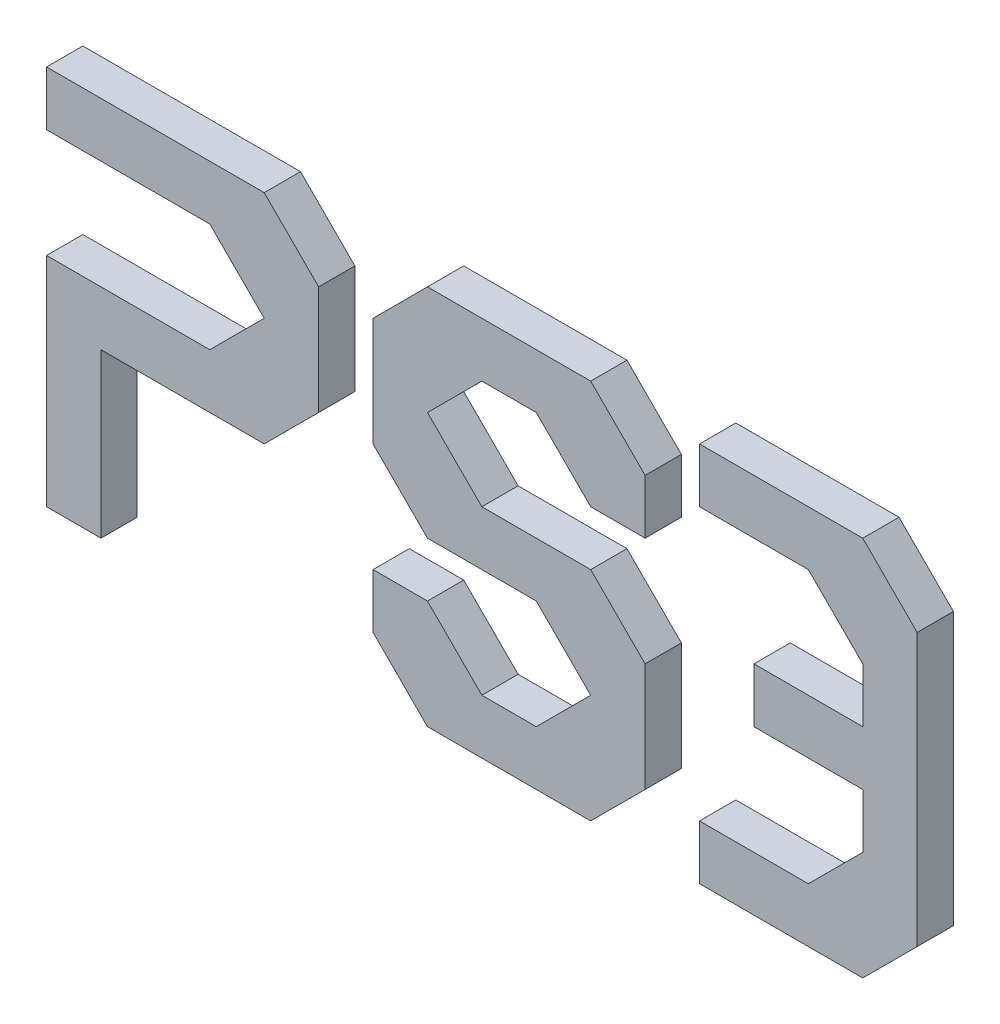
SolidWorks part; units mm, degrees
ref_plane "Front Plane" through (0, 0, 0) normal (0, 0, 1) x (1, 0, 0)
ref_plane "Top Plane" through (0, 0, 0) normal (0, 1, 0) x (1, 0, 0)
ref_plane "Right Plane" through (0, 0, 0) normal (1, 0, 0) x (0, 0, -1)
sketch "Sketch1" plane through (0, 0, 0) normal (0, 0, 1) x (1, 0, 0)
  line L0 (15, 15) -> (30, 15)
  line L1 (0, 0) -> (15, 0)
  line L2 (0, 0) -> (0, 15)
  line L3 (0, 15) -> (15, 15)
  line L4 (15, 0) -> (15, 15)
  line L5 (30, 0) -> (30, 15)
  line L6 (15, 0) -> (30, 0)
  line L7 (15, 0) -> (15, 15)
  line L8 (30, 15) -> (45, 15)
  line L9 (45, 0) -> (45, 15)
  line L10 (30, 0) -> (45, 0)
  line L11 (30, 0) -> (30, 15)
  line L12 (45, 15) -> (60, 15)
  line L13 (60, 0) -> (60, 15)
  line L14 (45, 0) -> (60, 0)
  line L15 (45, 0) -> (45, 15)
  line L16 (60, 15) -> (75, 15)
  line L17 (75, 0) -> (75, 15)
  line L18 (60, 0) -> (75, 0)
  line L19 (60, 0) -> (60, 15)
  line L20 (75, 15) -> (90, 15)
  line L21 (90, 0) -> (90, 15)
  line L22 (75, 0) -> (90, 0)
  line L23 (75, 0) -> (75, 15)
  line L24 (90, 15) -> (105, 15)
  line L25 (105, 0) -> (105, 15)
  line L26 (90, 0) -> (105, 0)
  line L27 (90, 0) -> (90, 15)
  line L28 (105, 15) -> (120, 15)
  line L29 (120, 0) -> (120, 15)
  line L30 (105, 0) -> (120, 0)
  line L31 (105, 0) -> (105, 15)
  line L32 (120, 15) -> (135, 15)
  line L33 (135, 0) -> (135, 15)
  line L34 (120, 0) -> (135, 0)
  line L35 (120, 0) -> (120, 15)
  line L36 (135, 15) -> (150, 15)
  line L37 (150, 0) -> (150, 15)
  line L38 (135, 0) -> (150, 0)
  line L39 (135, 0) -> (135, 15)
  line L40 (150, 15) -> (165, 15)
  line L41 (165, 0) -> (165, 15)
  line L42 (150, 0) -> (165, 0)
  line L43 (150, 0) -> (150, 15)
  line L44 (165, 15) -> (180, 15)
  line L45 (180, 0) -> (180, 15)
  line L46 (165, 0) -> (180, 0)
  line L47 (165, 0) -> (165, 15)
  line L48 (180, 15) -> (195, 15)
  line L49 (195, 0) -> (195, 15)
  line L50 (180, 0) -> (195, 0)
  line L51 (180, 0) -> (180, 15)
  line L52 (195, 15) -> (210, 15)
  line L53 (210, 0) -> (210, 15)
  line L54 (195, 0) -> (210, 0)
  line L55 (195, 0) -> (195, 15)
  line L56 (210, 15) -> (225, 15)
  line L57 (225, 0) -> (225, 15)
  line L58 (210, 0) -> (225, 0)
  line L59 (210, 0) -> (210, 15)
  line L60 (225, 15) -> (240, 15)
  line L61 (240, 0) -> (240, 15)
  line L62 (225, 0) -> (240, 0)
  line L63 (225, 0) -> (225, 15)
  line L64 (0, 30) -> (15, 30)
  line L65 (15, 15) -> (15, 30)
  line L66 (0, 15) -> (15, 15)
  line L67 (0, 15) -> (0, 30)
  line L68 (15, 30) -> (30, 30)
  line L69 (30, 15) -> (30, 30)
  line L70 (15, 15) -> (30, 15)
  line L71 (15, 15) -> (15, 30)
  line L72 (30, 30) -> (45, 30)
  line L73 (45, 15) -> (45, 30)
  line L74 (30, 15) -> (45, 15)
  line L75 (30, 15) -> (30, 30)
  line L76 (45, 30) -> (60, 30)
  line L77 (60, 15) -> (60, 30)
  line L78 (45, 15) -> (60, 15)
  line L79 (45, 15) -> (45, 30)
  line L80 (60, 30) -> (75, 30)
  line L81 (75, 15) -> (75, 30)
  line L82 (60, 15) -> (75, 15)
  line L83 (60, 15) -> (60, 30)
  line L84 (75, 30) -> (90, 30)
  line L85 (90, 15) -> (90, 30)
  line L86 (75, 15) -> (90, 15)
  line L87 (75, 15) -> (75, 30)
  line L88 (90, 30) -> (105, 30)
  line L89 (105, 15) -> (105, 30)
  line L90 (90, 15) -> (105, 15)
  line L91 (90, 15) -> (90, 30)
  line L92 (105, 30) -> (120, 30)
  line L93 (120, 15) -> (120, 30)
  line L94 (105, 15) -> (120, 15)
  line L95 (105, 15) -> (105, 30)
  line L96 (120, 30) -> (135, 30)
  line L97 (135, 15) -> (135, 30)
  line L98 (120, 15) -> (135, 15)
  line L99 (120, 15) -> (120, 30)
  line L100 (135, 30) -> (150, 30)
  line L101 (150, 15) -> (150, 30)
  line L102 (135, 15) -> (150, 15)
  line L103 (135, 15) -> (135, 30)
  line L104 (150, 30) -> (165, 30)
  line L105 (165, 15) -> (165, 30)
  line L106 (150, 15) -> (165, 15)
  line L107 (150, 15) -> (150, 30)
  line L108 (165, 30) -> (180, 30)
  line L109 (180, 15) -> (180, 30)
  line L110 (165, 15) -> (180, 15)
  line L111 (165, 15) -> (165, 30)
  line L112 (180, 30) -> (195, 30)
  line L113 (195, 15) -> (195, 30)
  line L114 (180, 15) -> (195, 15)
  line L115 (180, 15) -> (180, 30)
  line L116 (195, 30) -> (210, 30)
  line L117 (210, 15) -> (210, 30)
  line L118 (195, 15) -> (210, 15)
  line L119 (195, 15) -> (195, 30)
  line L120 (210, 30) -> (225, 30)
  line L121 (225, 15) -> (225, 30)
  line L122 (210, 15) -> (225, 15)
  line L123 (210, 15) -> (210, 30)
  line L124 (225, 30) -> (240, 30)
  line L125 (240, 15) -> (240, 30)
  line L126 (225, 15) -> (240, 15)
  line L127 (225, 15) -> (225, 30)
  line L128 (0, 45) -> (15, 45)
  line L129 (15, 30) -> (15, 45)
  line L130 (0, 30) -> (15, 30)
  line L131 (0, 30) -> (0, 45)
  line L132 (15, 45) -> (30, 45)
  line L133 (30, 30) -> (30, 45)
  line L134 (15, 30) -> (30, 30)
  line L135 (15, 30) -> (15, 45)
  line L136 (30, 45) -> (45, 45)
  line L137 (45, 30) -> (45, 45)
  line L138 (30, 30) -> (45, 30)
  line L139 (30, 30) -> (30, 45)
  line L140 (45, 45) -> (60, 45)
  line L141 (60, 30) -> (60, 45)
  line L142 (45, 30) -> (60, 30)
  line L143 (45, 30) -> (45, 45)
  line L144 (60, 45) -> (75, 45)
  line L145 (75, 30) -> (75, 45)
  line L146 (60, 30) -> (75, 30)
  line L147 (60, 30) -> (60, 45)
  line L148 (75, 45) -> (90, 45)
  line L149 (90, 30) -> (90, 45)
  line L150 (75, 30) -> (90, 30)
  line L151 (75, 30) -> (75, 45)
  line L152 (90, 45) -> (105, 45)
  line L153 (105, 30) -> (105, 45)
  line L154 (90, 30) -> (105, 30)
  line L155 (90, 30) -> (90, 45)
  line L156 (105, 45) -> (120, 45)
  line L157 (120, 30) -> (120, 45)
  line L158 (105, 30) -> (120, 30)
  line L159 (105, 30) -> (105, 45)
  line L160 (120, 45) -> (135, 45)
  line L161 (135, 30) -> (135, 45)
  line L162 (120, 30) -> (135, 30)
  line L163 (120, 30) -> (120, 45)
  line L164 (135, 45) -> (150, 45)
  line L165 (150, 30) -> (150, 45)
  line L166 (135, 30) -> (150, 30)
  line L167 (135, 30) -> (135, 45)
  line L168 (150, 45) -> (165, 45)
  line L169 (165, 30) -> (165, 45)
  line L170 (150, 30) -> (165, 30)
  line L171 (150, 30) -> (150, 45)
  line L172 (165, 45) -> (180, 45)
  line L173 (180, 30) -> (180, 45)
  line L174 (165, 30) -> (180, 30)
  line L175 (165, 30) -> (165, 45)
  line L176 (180, 45) -> (195, 45)
  line L177 (195, 30) -> (195, 45)
  line L178 (180, 30) -> (195, 30)
  line L179 (180, 30) -> (180, 45)
  line L180 (195, 45) -> (210, 45)
  line L181 (210, 30) -> (210, 45)
  line L182 (195, 30) -> (210, 30)
  line L183 (195, 30) -> (195, 45)
  line L184 (210, 45) -> (225, 45)
  line L185 (225, 30) -> (225, 45)
  line L186 (210, 30) -> (225, 30)
  line L187 (210, 30) -> (210, 45)
  line L188 (225, 45) -> (240, 45)
  line L189 (240, 30) -> (240, 45)
  line L190 (225, 30) -> (240, 30)
  line L191 (225, 30) -> (225, 45)
  line L192 (0, 60) -> (15, 60)
  line L193 (15, 45) -> (15, 60)
  line L194 (0, 45) -> (15, 45)
  line L195 (0, 45) -> (0, 60)
  line L196 (15, 60) -> (30, 60)
  line L197 (30, 45) -> (30, 60)
  line L198 (15, 45) -> (30, 45)
  line L199 (15, 45) -> (15, 60)
  line L200 (30, 60) -> (45, 60)
  line L201 (45, 45) -> (45, 60)
  line L202 (30, 45) -> (45, 45)
  line L203 (30, 45) -> (30, 60)
  line L204 (45, 60) -> (60, 60)
  line L205 (60, 45) -> (60, 60)
  line L206 (45, 45) -> (60, 45)
  line L207 (45, 45) -> (45, 60)
  line L208 (60, 60) -> (75, 60)
  line L209 (75, 45) -> (75, 60)
  line L210 (60, 45) -> (75, 45)
  line L211 (60, 45) -> (60, 60)
  line L212 (75, 60) -> (90, 60)
  line L213 (90, 45) -> (90, 60)
  line L214 (75, 45) -> (90, 45)
  line L215 (75, 45) -> (75, 60)
  line L216 (90, 60) -> (105, 60)
  line L217 (105, 45) -> (105, 60)
  line L218 (90, 45) -> (105, 45)
  line L219 (90, 45) -> (90, 60)
  line L220 (105, 60) -> (120, 60)
  line L221 (120, 45) -> (120, 60)
  line L222 (105, 45) -> (120, 45)
  line L223 (105, 45) -> (105, 60)
  line L224 (120, 60) -> (135, 60)
  line L225 (135, 45) -> (135, 60)
  line L226 (120, 45) -> (135, 45)
  line L227 (120, 45) -> (120, 60)
  line L228 (135, 60) -> (150, 60)
  line L229 (150, 45) -> (150, 60)
  line L230 (135, 45) -> (150, 45)
  line L231 (135, 45) -> (135, 60)
  line L232 (150, 60) -> (165, 60)
  line L233 (165, 45) -> (165, 60)
  line L234 (150, 45) -> (165, 45)
  line L235 (150, 45) -> (150, 60)
  line L236 (165, 60) -> (180, 60)
  line L237 (180, 45) -> (180, 60)
  line L238 (165, 45) -> (180, 45)
  line L239 (165, 45) -> (165, 60)
  line L240 (180, 60) -> (195, 60)
  line L241 (195, 45) -> (195, 60)
  line L242 (180, 45) -> (195, 45)
  line L243 (180, 45) -> (180, 60)
  line L244 (195, 60) -> (210, 60)
  line L245 (210, 45) -> (210, 60)
  line L246 (195, 45) -> (210, 45)
  line L247 (195, 45) -> (195, 60)
  line L248 (210, 60) -> (225, 60)
  line L249 (225, 45) -> (225, 60)
  line L250 (210, 45) -> (225, 45)
  line L251 (210, 45) -> (210, 60)
  line L252 (225, 60) -> (240, 60)
  line L253 (240, 45) -> (240, 60)
  line L254 (225, 45) -> (240, 45)
  line L255 (225, 45) -> (225, 60)
  line L256 (0, 75) -> (15, 75)
  line L257 (15, 60) -> (15, 75)
  line L258 (0, 60) -> (15, 60)
  line L259 (0, 60) -> (0, 75)
  line L260 (15, 75) -> (30, 75)
  line L261 (30, 60) -> (30, 75)
  line L262 (15, 60) -> (30, 60)
  line L263 (15, 60) -> (15, 75)
  line L264 (30, 75) -> (45, 75)
  line L265 (45, 60) -> (45, 75)
  line L266 (30, 60) -> (45, 60)
  line L267 (30, 60) -> (30, 75)
  line L268 (45, 75) -> (60, 75)
  line L269 (60, 60) -> (60, 75)
  line L270 (45, 60) -> (60, 60)
  line L271 (45, 60) -> (45, 75)
  line L272 (60, 75) -> (75, 75)
  line L273 (75, 60) -> (75, 75)
  line L274 (60, 60) -> (75, 60)
  line L275 (60, 60) -> (60, 75)
  line L276 (75, 75) -> (90, 75)
  line L277 (90, 60) -> (90, 75)
  line L278 (75, 60) -> (90, 60)
  line L279 (75, 60) -> (75, 75)
  line L280 (90, 75) -> (105, 75)
  line L281 (105, 60) -> (105, 75)
  line L282 (90, 60) -> (105, 60)
  line L283 (90, 60) -> (90, 75)
  line L284 (105, 75) -> (120, 75)
  line L285 (120, 60) -> (120, 75)
  line L286 (105, 60) -> (120, 60)
  line L287 (105, 60) -> (105, 75)
  line L288 (120, 75) -> (135, 75)
  line L289 (135, 60) -> (135, 75)
  line L290 (120, 60) -> (135, 60)
  line L291 (120, 60) -> (120, 75)
  line L292 (135, 75) -> (150, 75)
  line L293 (150, 60) -> (150, 75)
  line L294 (135, 60) -> (150, 60)
  line L295 (135, 60) -> (135, 75)
  line L296 (150, 75) -> (165, 75)
  line L297 (165, 60) -> (165, 75)
  line L298 (150, 60) -> (165, 60)
  line L299 (150, 60) -> (150, 75)
  line L300 (165, 75) -> (180, 75)
  line L301 (180, 60) -> (180, 75)
  line L302 (165, 60) -> (180, 60)
  line L303 (165, 60) -> (165, 75)
  line L304 (180, 75) -> (195, 75)
  line L305 (195, 60) -> (195, 75)
  line L306 (180, 60) -> (195, 60)
  line L307 (180, 60) -> (180, 75)
  line L308 (195, 75) -> (210, 75)
  line L309 (210, 60) -> (210, 75)
  line L310 (195, 60) -> (210, 60)
  line L311 (195, 60) -> (195, 75)
  line L312 (210, 75) -> (225, 75)
  line L313 (225, 60) -> (225, 75)
  line L314 (210, 60) -> (225, 60)
  line L315 (210, 60) -> (210, 75)
  line L316 (225, 75) -> (240, 75)
  line L317 (240, 60) -> (240, 75)
  line L318 (225, 60) -> (240, 60)
  line L319 (225, 60) -> (225, 75)
  line L320 (0, 90) -> (15, 90)
  line L321 (15, 75) -> (15, 90)
  line L322 (0, 75) -> (15, 75)
  line L323 (0, 75) -> (0, 90)
  line L324 (15, 90) -> (30, 90)
  line L325 (30, 75) -> (30, 90)
  line L326 (15, 75) -> (30, 75)
  line L327 (15, 75) -> (15, 90)
  line L328 (30, 90) -> (45, 90)
  line L329 (45, 75) -> (45, 90)
  line L330 (30, 75) -> (45, 75)
  line L331 (30, 75) -> (30, 90)
  line L332 (45, 90) -> (60, 90)
  line L333 (60, 75) -> (60, 90)
  line L334 (45, 75) -> (60, 75)
  line L335 (45, 75) -> (45, 90)
  line L336 (60, 90) -> (75, 90)
  line L337 (75, 75) -> (75, 90)
  line L338 (60, 75) -> (75, 75)
  line L339 (60, 75) -> (60, 90)
  line L340 (75, 90) -> (90, 90)
  line L341 (90, 75) -> (90, 90)
  line L342 (75, 75) -> (90, 75)
  line L343 (75, 75) -> (75, 90)
  line L344 (90, 90) -> (105, 90)
  line L345 (105, 75) -> (105, 90)
  line L346 (90, 75) -> (105, 75)
  line L347 (90, 75) -> (90, 90)
  line L348 (105, 90) -> (120, 90)
  line L349 (120, 75) -> (120, 90)
  line L350 (105, 75) -> (120, 75)
  line L351 (105, 75) -> (105, 90)
  line L352 (120, 90) -> (135, 90)
  line L353 (135, 75) -> (135, 90)
  line L354 (120, 75) -> (135, 75)
  line L355 (120, 75) -> (120, 90)
  line L356 (135, 90) -> (150, 90)
  line L357 (150, 75) -> (150, 90)
  line L358 (135, 75) -> (150, 75)
  line L359 (135, 75) -> (135, 90)
  line L360 (150, 90) -> (165, 90)
  line L361 (165, 75) -> (165, 90)
  line L362 (150, 75) -> (165, 75)
  line L363 (150, 75) -> (150, 90)
  line L364 (165, 90) -> (180, 90)
  line L365 (180, 75) -> (180, 90)
  line L366 (165, 75) -> (180, 75)
  line L367 (165, 75) -> (165, 90)
  line L368 (180, 90) -> (195, 90)
  line L369 (195, 75) -> (195, 90)
  line L370 (180, 75) -> (195, 75)
  line L371 (180, 75) -> (180, 90)
  line L372 (195, 90) -> (210, 90)
  line L373 (210, 75) -> (210, 90)
  line L374 (195, 75) -> (210, 75)
  line L375 (195, 75) -> (195, 90)
  line L376 (210, 90) -> (225, 90)
  line L377 (225, 75) -> (225, 90)
  line L378 (210, 75) -> (225, 75)
  line L379 (210, 75) -> (210, 90)
  line L380 (225, 90) -> (240, 90)
  line L381 (240, 75) -> (240, 90)
  line L382 (225, 75) -> (240, 75)
  line L383 (225, 75) -> (225, 90)
  line L384 (0, 105) -> (15, 105)
  line L385 (15, 90) -> (15, 105)
  line L386 (0, 90) -> (15, 90)
  line L387 (0, 90) -> (0, 105)
  line L388 (15, 105) -> (30, 105)
  line L389 (30, 90) -> (30, 105)
  line L390 (15, 90) -> (30, 90)
  line L391 (15, 90) -> (15, 105)
  line L392 (30, 105) -> (45, 105)
  line L393 (45, 90) -> (45, 105)
  line L394 (30, 90) -> (45, 90)
  line L395 (30, 90) -> (30, 105)
  line L396 (45, 105) -> (60, 105)
  line L397 (60, 90) -> (60, 105)
  line L398 (45, 90) -> (60, 90)
  line L399 (45, 90) -> (45, 105)
  line L400 (60, 105) -> (75, 105)
  line L401 (75, 90) -> (75, 105)
  line L402 (60, 90) -> (75, 90)
  line L403 (60, 90) -> (60, 105)
  line L404 (75, 105) -> (90, 105)
  line L405 (90, 90) -> (90, 105)
  line L406 (75, 90) -> (90, 90)
  line L407 (75, 90) -> (75, 105)
  line L408 (90, 105) -> (105, 105)
  line L409 (105, 90) -> (105, 105)
  line L410 (90, 90) -> (105, 90)
  line L411 (90, 90) -> (90, 105)
  line L412 (105, 105) -> (120, 105)
  line L413 (120, 90) -> (120, 105)
  line L414 (105, 90) -> (120, 90)
  line L415 (105, 90) -> (105, 105)
  line L416 (120, 105) -> (135, 105)
  line L417 (135, 90) -> (135, 105)
  line L418 (120, 90) -> (135, 90)
  line L419 (120, 90) -> (120, 105)
  line L420 (135, 105) -> (150, 105)
  line L421 (150, 90) -> (150, 105)
  line L422 (135, 90) -> (150, 90)
  line L423 (135, 90) -> (135, 105)
  line L424 (150, 105) -> (165, 105)
  line L425 (165, 90) -> (165, 105)
  line L426 (150, 90) -> (165, 90)
  line L427 (150, 90) -> (150, 105)
  line L428 (165, 105) -> (180, 105)
  line L429 (180, 90) -> (180, 105)
  line L430 (165, 90) -> (180, 90)
  line L431 (165, 90) -> (165, 105)
  line L432 (180, 105) -> (195, 105)
  line L433 (195, 90) -> (195, 105)
  line L434 (180, 90) -> (195, 90)
  line L435 (180, 90) -> (180, 105)
  line L436 (195, 105) -> (210, 105)
  line L437 (210, 90) -> (210, 105)
  line L438 (195, 90) -> (210, 90)
  line L439 (195, 90) -> (195, 105)
  line L440 (210, 105) -> (225, 105)
  line L441 (225, 90) -> (225, 105)
  line L442 (210, 90) -> (225, 90)
  line L443 (210, 90) -> (210, 105)
  line L444 (225, 105) -> (240, 105)
  line L445 (240, 90) -> (240, 105)
  line L446 (225, 90) -> (240, 90)
  line L447 (225, 90) -> (225, 105)
  dimension "D1" = 15
  dimension "D2" = 15
sketch "Sketch2" plane through (0, 0, 0) normal (0, 0, 1) x (1, 0, 0)
  line L0 (0, 90) -> (0, 105)
  line L1 (0, 105) -> (45, 105)
  line L2 (60, 105) -> (75, 90)
  line L3 (75, 90) -> (75, 60)
  line L4 (75, 60) -> (60, 45)
  line L5 (45, 45) -> (15, 45)
  line L6 (15, 45) -> (15, 0)
  line L7 (15, 0) -> (0, 0)
  line L8 (0, 0) -> (0, 60)
  line L9 (0, 60) -> (30, 60)
  line L10 (45, 60) -> (60, 75)
  line L11 (60, 75) -> (45, 90)
  line L12 (30, 90) -> (0, 90)
  line L13 (105, 30) -> (90, 30)
  line L14 (90, 30) -> (90, 15)
  line L15 (90, 15) -> (105, 0)
  line L16 (105, 0) -> (150, 0)
  line L17 (150, 0) -> (165, 15)
  line L18 (165, 15) -> (165, 45)
  line L19 (165, 45) -> (150, 60)
  line L20 (150, 60) -> (135, 60)
  line L21 (135, 60) -> (120, 60)
  line L22 (120, 60) -> (105, 75)
  line L23 (105, 75) -> (120, 90)
  line L24 (120, 90) -> (135, 90)
  line L25 (135, 90) -> (150, 75)
  line L26 (150, 75) -> (165, 75)
  line L27 (165, 75) -> (165, 90)
  line L28 (165, 90) -> (150, 105)
  line L29 (150, 105) -> (105, 105)
  line L30 (105, 105) -> (90, 90)
  line L31 (90, 90) -> (90, 60)
  line L32 (90, 60) -> (105, 45)
  line L33 (105, 45) -> (135, 45)
  line L34 (135, 45) -> (150, 30)
  line L35 (150, 30) -> (135, 15)
  line L36 (135, 15) -> (120, 15)
  line L37 (120, 15) -> (105, 30)
  line L38 (45, 105) -> (60, 105)
  line L39 (30, 90) -> (45, 90)
  line L40 (30, 60) -> (45, 60)
  line L41 (45, 45) -> (60, 45)
  line L42 (180, 15) -> (180, 0)
  line L43 (180, 0) -> (225, 0)
  line L44 (225, 0) -> (240, 15)
  line L45 (240, 15) -> (240, 90)
  line L46 (240, 90) -> (225, 105)
  line L47 (225, 105) -> (180, 105)
  line L48 (180, 105) -> (180, 90)
  line L49 (180, 90) -> (210, 90)
  line L50 (210, 90) -> (225, 75)
  line L51 (225, 75) -> (225, 60)
  line L52 (225, 60) -> (195, 60)
  line L53 (195, 60) -> (195, 45)
  line L54 (195, 45) -> (225, 45)
  line L55 (225, 45) -> (225, 30)
  line L56 (225, 30) -> (210, 15)
  line L57 (210, 15) -> (180, 15)
extrude "Extrude1" add sketch "Sketch2" along normal blind 10
